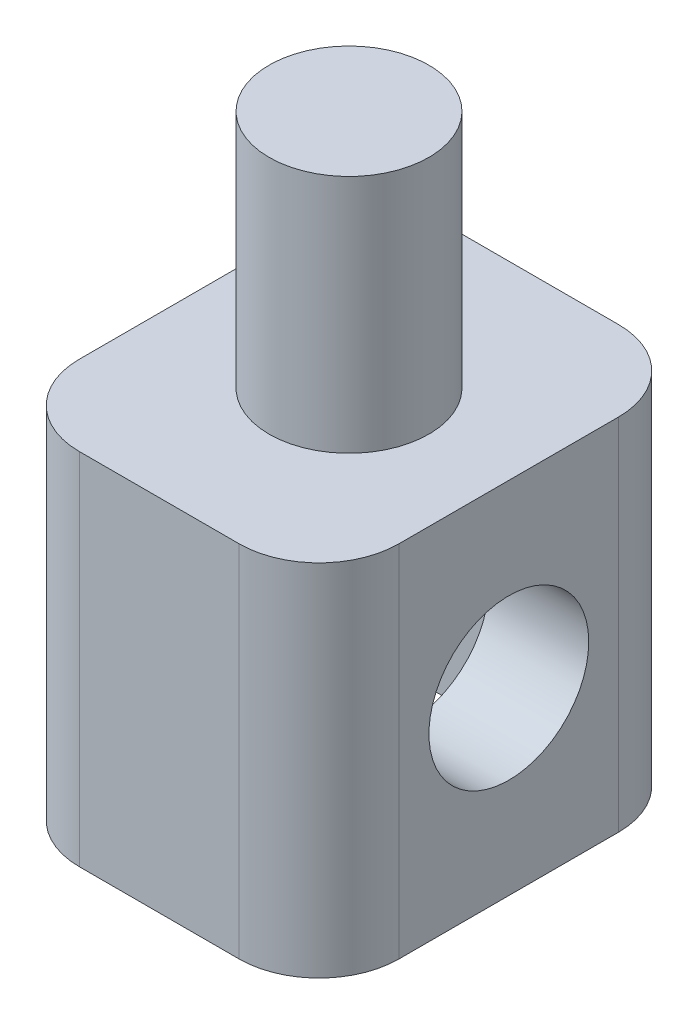
SolidWorks part; units mm, degrees
ref_plane "Front Plane" through (0, 0, 0) normal (0, 0, 1) x (1, 0, 0)
ref_plane "Top Plane" through (0, 0, 0) normal (0, 1, 0) x (1, 0, 0)
ref_plane "Right Plane" through (0, 0, 0) normal (1, 0, 0) x (0, 0, -1)
sketch "Sketch1" plane through (0, 0, 0) normal (0, 1, 0) x (1, 0, 0)
  line L1 (4, -4.75) -> (-4, -4.75)
  line L2 (4, -4.75) -> (4, 4.75)
  line L3 (4, 4.75) -> (-4, 4.75)
  line L4 (-4, -4.75) -> (-4, 4.75)
  line L5 (4, -4.75) -> (-4, 4.75) construction
  line L6 (4, 4.75) -> (-4, -4.75) construction
  point P0 (0, 0)
extrude "Boss-Extrude1" add sketch "Sketch1" along normal mid plane 9
sketch "Sketch2" plane through (0, 4.5, 0) normal (0, 1, 0) x (1, 0, 0)
  circle A0 centre (0, 0) radius 2
extrude "Boss-Extrude2" add sketch "Sketch2" along normal blind 6
sketch "Sketch5" plane through (0, 0, 0) normal (1, 0, 0) x (0, 0, -1)
  line L0 (-3.5, -2.0207) -> (-3.5, -4.5)
  line L1 (0, 4.0415) -> (-3.5, 2.0207)
  line L2 (-3.5, 2.0207) -> (-3.5, -2.0207)
  line L5 (3.5, -2.0207) -> (3.5, 2.0207)
  line L6 (3.5, 2.0207) -> (0, 4.0415)
  line L8 (-4.75, -4.5) -> (4.75, -4.5) construction
  line L9 (-3.5, -4.5) -> (3.5, -4.5)
  line L10 (3.5, -4.5) -> (3.5, -2.0207)
  line L15 (0, -4.0415) -> (3.5, -2.0207) [skipped]
  line L16 (-3.5, -2.0207) -> (0, -4.0415) [skipped]
  circle A0 centre (0, 0) radius 3.5 construction
extrude "Cut-Extrude1" cut sketch "Sketch5" against normal mid plane 3
sketch "Sketch6" plane through (4, 0, 0) normal (1, 0, 0) x (0, 0, -1)
  circle A0 centre (0, 0) radius 2
extrude "Cut-Extrude2" cut sketch "Sketch6" against normal through all
fillet "Fillet1" radius 2 4 edges at (4, 0, -4.75) (-4, 0, -4.75) (-4, 0, 4.75) (4, 0, 4.75)
